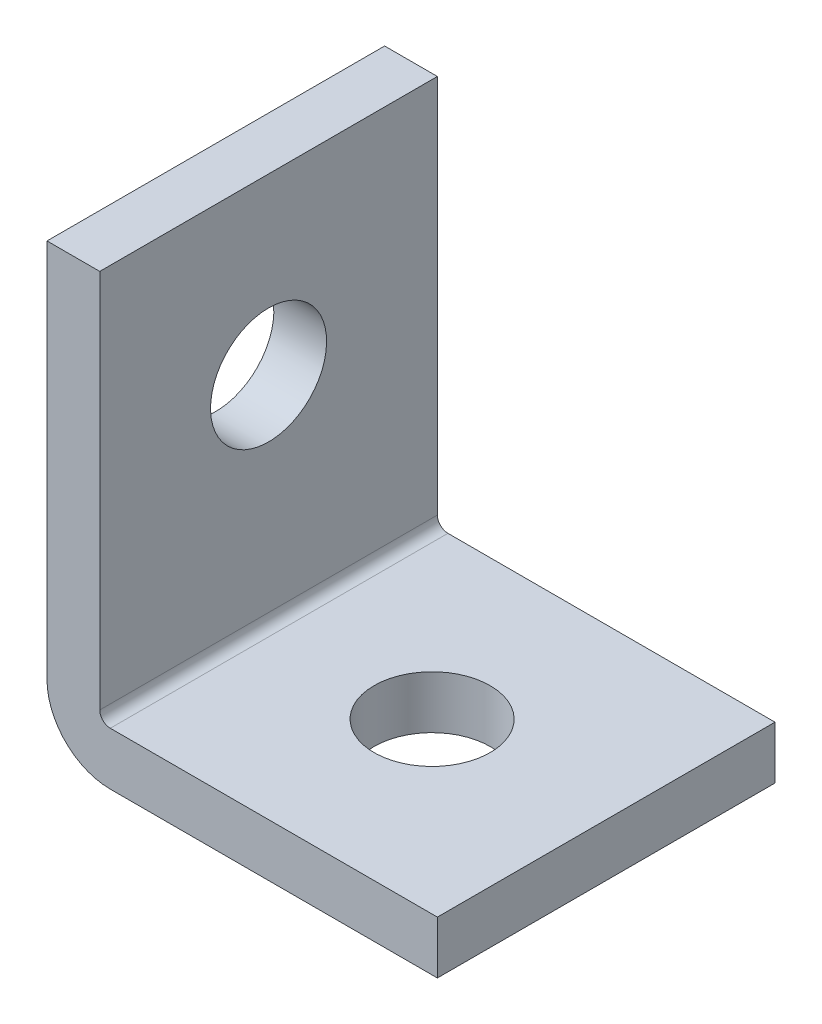
SolidWorks part; units mm, degrees
ref_plane "Front Plane" through (0, 0, 0) normal (0, 0, 1) x (1, 0, 0)
ref_plane "Top Plane" through (0, 0, 0) normal (0, 1, 0) x (1, 0, 0)
ref_plane "Right Plane" through (0, 0, 0) normal (1, 0, 0) x (0, 0, -1)
sketch "Sketch1" plane through (0, 0, 0) normal (0, 0, 1) x (1, 0, 0)
  line L0 (0, 1.27) -> (0, 46.99)
  line L1 (0, 46.99) -> (-6.35, 46.99)
  line L2 (-6.35, 46.99) -> (-6.35, 1.27)
  line L3 (1.27, -6.35) -> (40.64, -6.35)
  line L4 (40.64, -6.35) -> (40.64, 0)
  line L5 (40.64, 0) -> (1.27, 0)
  arc A0 (-6.35, 1.27) -> (1.27, -6.35) centre (1.27, 1.27) ccw
  arc A1 (0, 1.27) -> (1.27, 0) centre (1.27, 1.27) ccw
  point P12 (0, 0)
  dimension "D4" = 7.62
  dimension "D5" = 1.27
  dimension "D1" = 6.35
  dimension "D2" = 53.34
  dimension "D3" = 46.99
extrude "Boss-Extrude1" add sketch "Sketch1" along normal mid plane 40.64
sketch "Sketch2" plane through (0, 0, 0) normal (1, 0, 0) x (0, 0, -1)
  line L0 (-20.32, 46.99) -> (20.32, 46.99) construction
  circle A0 centre (0, 26.035) radius 6.985
  dimension "D1" = 13.97
  dimension "D2" = 13.97
extrude "Cut-Extrude1" cut sketch "Sketch2" against normal up to next
sketch "Sketch3" plane through (0, 0, 0) normal (0, 1, 0) x (1, 0, 0)
  line L0 (40.64, -20.32) -> (40.64, 20.32) construction
  circle A0 centre (19.685, 0) radius 6.985
  dimension "D1" = 13.97
  dimension "D2" = 13.97
extrude "Cut-Extrude2" cut sketch "Sketch3" against normal up to next
